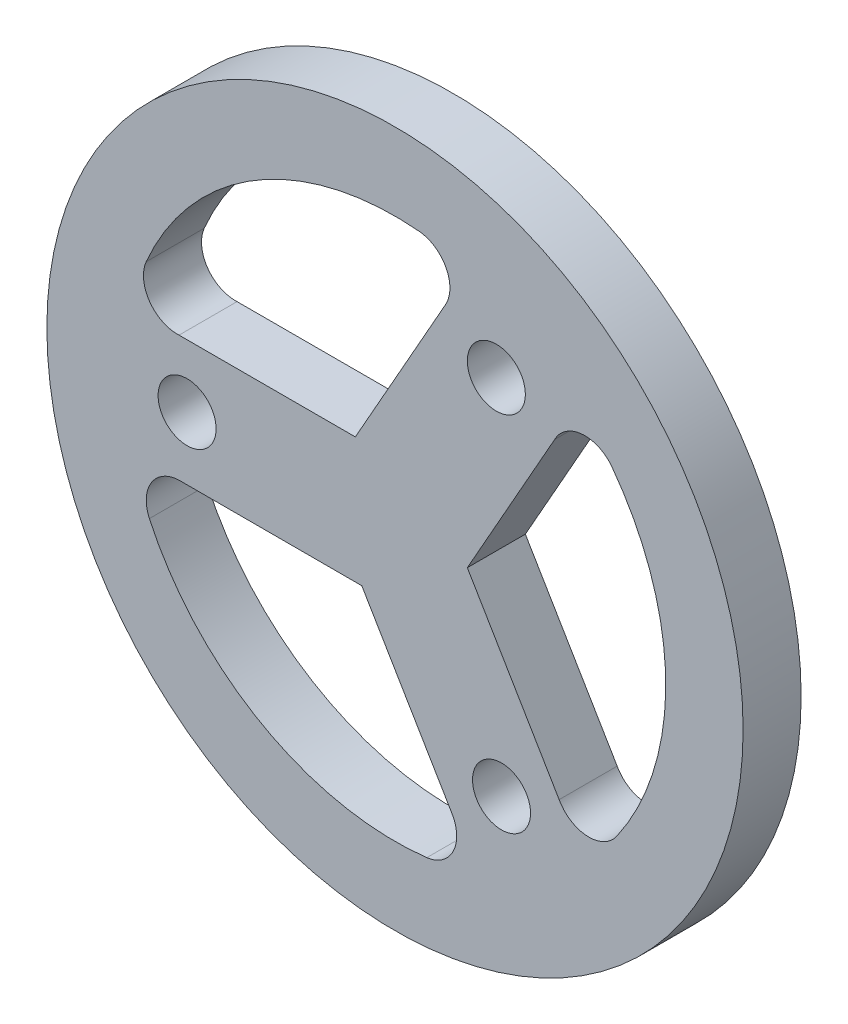
SolidWorks part; units mm, degrees
ref_plane "Plan de face" through (0, 0, 0) normal (0, 0, 1) x (1, 0, 0)
ref_plane "Plan de dessus" through (0, 0, 0) normal (0, 1, 0) x (1, 0, 0)
ref_plane "Plan de droite" through (0, 0, 0) normal (1, 0, 0) x (0, 0, -1)
sketch "Esquisse1" plane through (0, 0, 0) normal (0, 0, 1) x (1, 0, 0)
  line L0 (5.2405, 9.3862) -> (3.778, 6.7668) construction
  line L1 (-11.0721, -3.4075) -> (-1.7167, -3.4097)
  line L2 (-11.1656, 3.0874) -> (-2.0501, 3.0874)
  line L3 (2.777, -10.9906) -> (-1.7167, -3.4097)
  line L4 (8.487, -7.885) -> (3.7403, 0.1271)
  line L5 (8.2566, 8.126) -> (3.7403, 0.1271)
  line L6 (2.5851, 11.2925) -> (-2.0501, 3.0874)
  circle A0 centre (0, 0) radius 18
  circle A9 centre (5.2405, 9.3862) radius 1.5
  arc A22 (11.4536, -8.0507) -> (11.2172, 8.3771) centre (0, 0) ccw
  arc A25 (8.487, -7.885) -> (11.4536, -8.0507) centre (10.0219, -7.0444) ccw
  arc A29 (2.5851, 11.2925) -> (1.2453, 13.9445) centre (1.0897, 12.2014) ccw
  arc A30 (11.2172, 8.3771) -> (8.2566, 8.126) centre (9.815, 7.3299) ccw
  arc A31 (1.2453, 13.9445) -> (-12.8633, 5.5258) centre (0, 0) ccw
  arc A32 (-12.699, -5.8938) -> (1.6462, -13.9029) centre (0, 0) ccw
  arc A35 (2.777, -10.9906) -> (2.909, -11.2134) centre (5.6365, -9.4461) ccw
  circle A36 centre (5.5084, -9.2314) radius 1.5
  arc A38 (1.6462, -13.9029) -> (2.909, -11.2134) centre (1.4404, -12.165) ccw
  arc A39 (-11.0721, -3.4075) -> (-12.699, -5.8938) centre (-11.1116, -5.157) ccw
  circle A40 centre (-10.7489, -0.1547) radius 1.5
  arc A42 (-12.8633, 5.5258) -> (-11.1656, 3.0874) centre (-11.2554, 4.8351) ccw
  point P32 (0, 0)
  point P37 (0, 0)
  point P40 (0, 0)
  point P49 (0, 0)
  dimension "D1" = 36
  dimension "D2" = 10.7489
  dimension "D3" = 3
  dimension "D4" = 6.4949
  dimension "D11" = 3
  dimension "D14" = 28
  dimension "D13" = 1.75
  dimension "D15" = 1.75
  dimension "D16" = 16.4295
  dimension "D6" = 10.75
  dimension "D8" = 3.2528
extrude "Boss.-Extru.1" add sketch "Esquisse1" along normal blind 3
